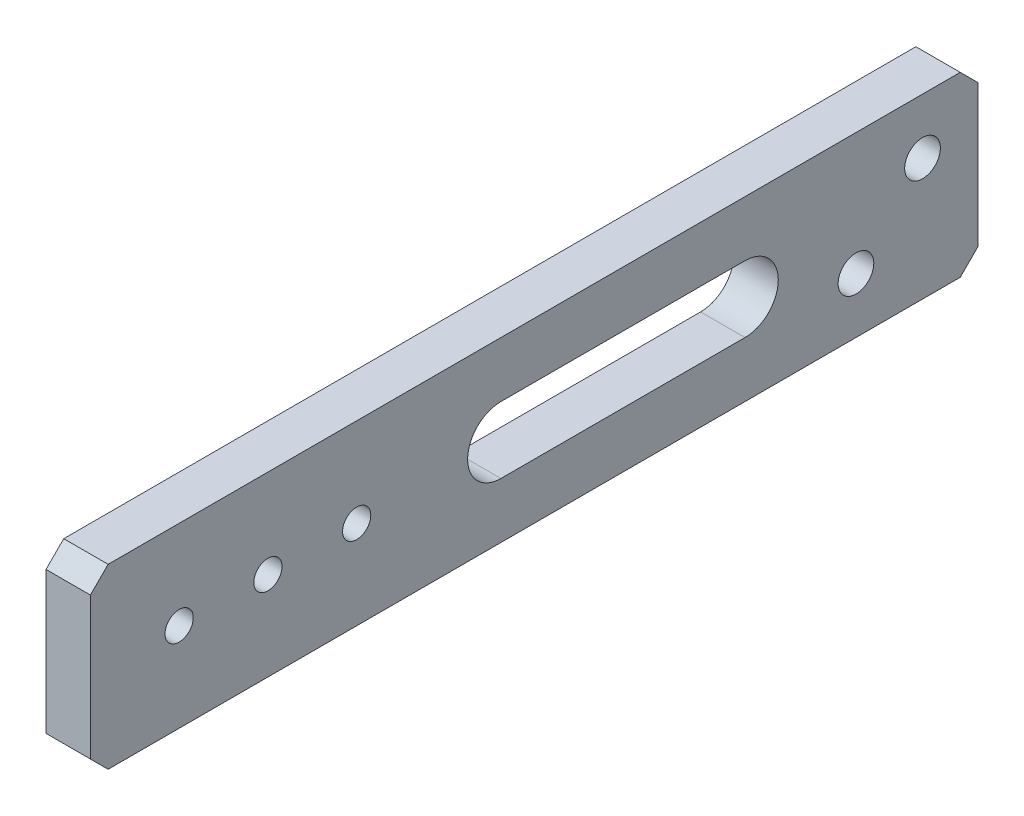
SolidWorks part; units mm, degrees
material "6061-T6 (SS)"
ref_plane "Front" through (0, 0, 0) normal (0, 0, 1) x (1, 0, 0)
ref_plane "Top" through (0, 0, 0) normal (0, 1, 0) x (1, 0, 0)
ref_plane "Right" through (0, 0, 0) normal (1, 0, 0) x (0, 0, -1)
sketch "Sketch1" plane through (0, 0, 0) normal (1, 0, 0) x (0, 0, -1)
  line L1 (0, 0) -> (127, 0)
  line L2 (0, 0) -> (0, 25.4)
  line L3 (0, 25.4) -> (127, 25.4)
  line L6 (127, 25.4) -> (127, 0)
  dimension "D1" = 25.4
  dimension "D2" = 127
extrude "Boss-Extrude1" add sketch "Sketch1" along normal blind 6.35
hole_wizard "#10-32 Tapped Hole1" positions "Sketch2" profile "Sketch3" tap size "#10-32" standard "ANSI Inch" end condition through all
sketch "Sketch2" plane through (6.35, 0, 0) normal (1, 0, 0) x (0, 0, -1)
  line L0 (0, 0) -> (12.7, 12.7) construction
  line L1 (12.7, 12.7) -> (25.4, 12.7) construction
  line L2 (25.4, 12.7) -> (38.1, 12.7) construction
  line L3 (38.1, 12.7) -> (50.8, 25.4) construction
  line L4 (127, 25.4) -> (0, 25.4) construction
  line L6 (0, 25.4) -> (0, 0) construction
  point P0 (12.7, 12.7)
  point P2 (25.4, 12.7)
  point P4 (38.1, 12.7)
  dimension "D1" = 50.8
  dimension "D2" = 12.7
sketch "Sketch3" plane through (6.35, 12.7, -12.7) normal (0, 1, 0) x (0, 0, -1)
  line L0 (0, 0) -> (0, 6.35)
  line L1 (0, 6.35) -> (2.0193, 6.35)
  line L2 (2.0193, 6.35) -> (2.0193, 0)
  line L5 (2.0193, 0) -> (0, 0)
  line L11 (0, -6.35) -> (0, 107.95) construction
  dimension "Thru Tap Drill Dia." = 4.0386
  dimension "Thru Tap Drill Depth" = 6.35
cosmetic thread "Hole Thread1" parameters "D2"=4.826
cosmetic thread "Hole Thread2" parameters "D2"=4.826
cosmetic thread "Hole Thread3" parameters "D2"=4.826
hole_wizard "#10 Clearance Hole1" positions "Sketch4" profile "Sketch5" hole size "#10" standard "ANSI Inch" end condition through all
sketch "Sketch4" plane through (6.35, 0, 0) normal (1, 0, 0) x (0, 0, -1)
  line L0 (101.6, 0) -> (109.5375, 7.9375) construction
  line L1 (0, 0) -> (127, 0) construction
  line L2 (109.5375, 7.9375) -> (119.0625, 17.4625) construction
  line L3 (119.0625, 17.4625) -> (127, 25.4) construction
  line L5 (127, 0) -> (127, 25.4) construction
  point P13 (119.0625, 17.4625)
  point P15 (109.5375, 7.9375)
  dimension "D1" = 25.4
  dimension "D2" = 9.525
sketch "Sketch5" plane through (6.35, 17.4625, -119.0625) normal (0, 1, 0) x (0, 0, -1)
  line L0 (0, 0) -> (0, 6.35)
  line L1 (0, 6.35) -> (2.5527, 6.35)
  line L2 (2.5527, 6.35) -> (2.5527, 0)
  line L5 (2.5527, 0) -> (0, 0)
  line L11 (0, -6.35) -> (0, 107.95) construction
  dimension "Thru Hole Dia." = 5.1054
  dimension "Thru Hole Depth" = 6.35
chamfer "Chamfer1" distance 2.54 angle 45 4 edges at (3.175, 25.4, 0) (3.175, 25.4, -127) (3.175, 0, -127) (3.175, 0, 0)
sketch "Sketch6" plane through (6.35, 0, 0) normal (1, 0, 0) x (0, 0, -1)
  line L0 (93.6625, 12.7) -> (58.7375, 12.7) construction
  line L1 (93.6625, 7.9375) -> (58.7375, 7.9375)
  line L2 (93.6625, 17.4625) -> (58.7375, 17.4625)
  line L3 (2.54, 0) -> (124.46, 0) construction
  line L4 (0, 22.86) -> (0, 2.54) construction
  line L5 (127, 2.54) -> (127, 22.86) construction
  arc A0 (93.6625, 7.9375) -> (93.6625, 17.4625) centre (93.6625, 12.7) ccw
  arc A1 (58.7375, 17.4625) -> (58.7375, 7.9375) centre (58.7375, 12.7) ccw
  point P2 (76.2, 12.7)
  dimension "D3" = 53.975
  dimension "D1" = 12.7
  dimension "D2" = 9.525
  dimension "D4" = 28.575
extrude "Cut-Extrude1" cut sketch "Sketch6" against normal through all
